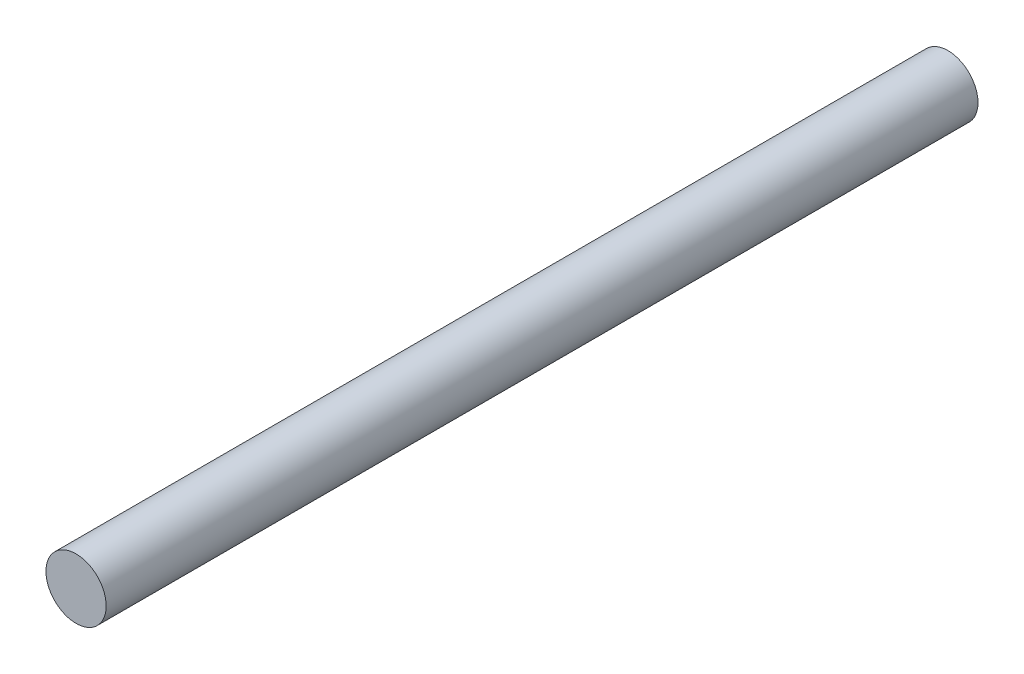
SolidWorks part; units mm, degrees
ref_plane "Front Plane" through (0, 0, 0) normal (0, 0, 1) x (1, 0, 0)
ref_plane "Top Plane" through (0, 0, 0) normal (0, 1, 0) x (1, 0, 0)
ref_plane "Right Plane" through (0, 0, 0) normal (1, 0, 0) x (0, 0, -1)
sketch "Sketch1" plane through (0, 0, 0) normal (0, 0, 1) x (1, 0, 0)
  circle A0 centre (0, 0) radius 3.8
  dimension "D1" = 7.6
extrude "Boss-Extrude1" add sketch "Sketch1" along normal blind 110
